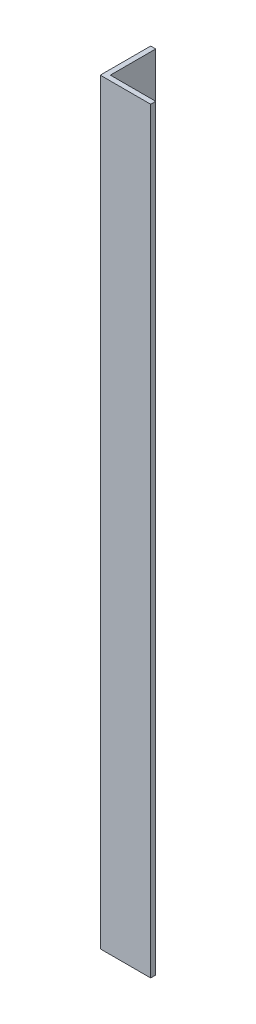
SolidWorks part; units mm, degrees
ref_plane "Спереди" through (0, 0, 0) normal (0, 0, 1) x (1, 0, 0)
ref_plane "Сверху" through (0, 0, 0) normal (0, 1, 0) x (1, 0, 0)
ref_plane "Справа" through (0, 0, 0) normal (1, 0, 0) x (0, 0, -1)
sketch "Эскиз1" plane through (0, 0, 0) normal (0, 1, 0) x (1, 0, 0)
  line L0 (0, 40) -> (0, 0)
  line L1 (0, 0) -> (40, 0)
extrude "Вытянуть-Тонкостенный1" add sketch "Эскиз1" along normal blind 600 thin thin type one direction reverse wall 4
